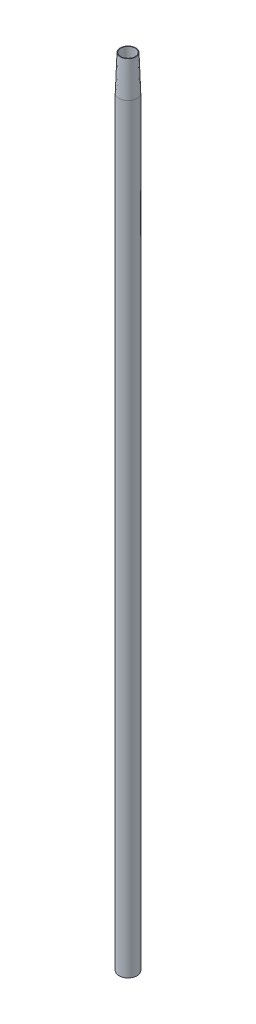
SolidWorks part; units mm, degrees
ref_plane "Front Plane" through (0, 0, 0) normal (0, 0, 1) x (1, 0, 0)
ref_plane "Top Plane" through (0, 0, 0) normal (0, 1, 0) x (1, 0, 0)
ref_plane "Right Plane" through (0, 0, 0) normal (1, 0, 0) x (0, 0, -1)
sketch "Sketch1" plane through (0, 0, 0) normal (0, 1, 0) x (1, 0, 0)
  circle A0 centre (0, 0) radius 2.555
  circle A1 centre (0, 0) radius 2.055
  dimension "D1" = 0.5
  dimension "D2" = 5.11
extrude "Boss-Extrude1" add sketch "Sketch1" along normal blind 225
chamfer "Chamfer1" distance 10 angle 2 1 edges at (0, 225, 2.555)
